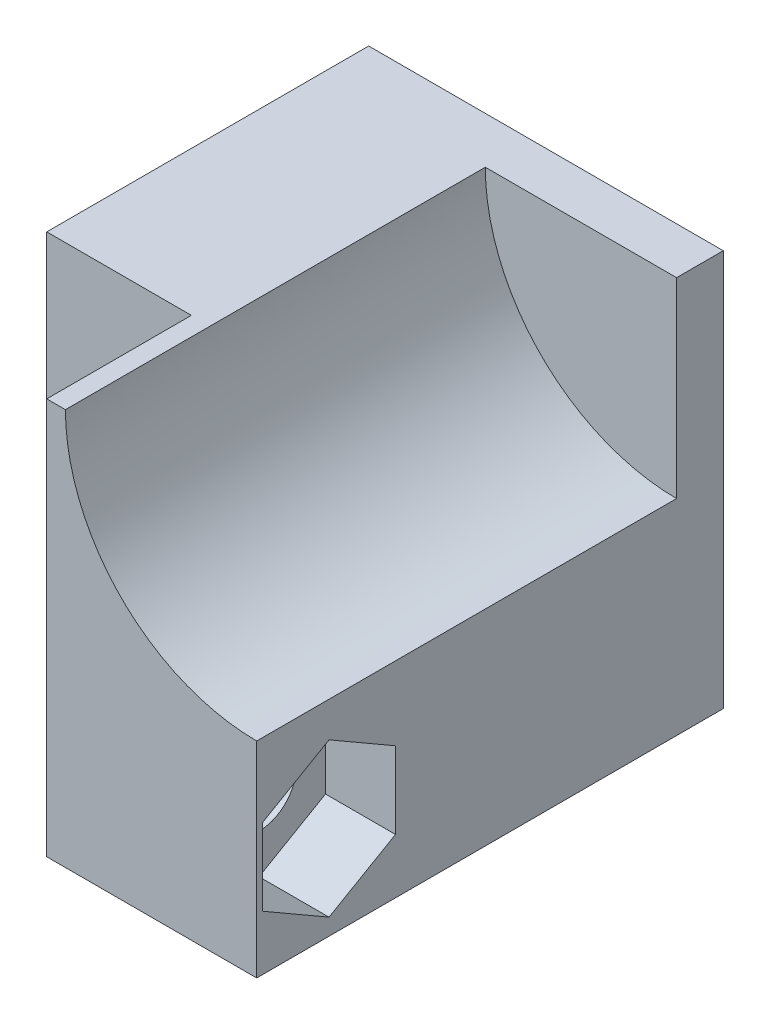
SolidWorks part; units mm, degrees
ref_plane "Alzado" through (0, 0, 0) normal (0, 0, 1) x (1, 0, 0)
ref_plane "Planta" through (0, 0, 0) normal (0, 1, 0) x (1, 0, 0)
ref_plane "Vista lateral" through (0, 0, 0) normal (1, 0, 0) x (0, 0, -1)
sketch "Croquis1" plane through (0, 0, 0) normal (0, 0, 1) x (1, 0, 0)
  line L1 (0, 0) -> (15.2, 0)
  line L2 (0, 0) -> (0, 17)
  line L3 (0, 17) -> (15.2, 17)
  line L4 (15.2, 0) -> (15.2, 17)
  dimension "D1" = 15.2
  dimension "D2" = 17
extrude "Saliente-Extruir1" add sketch "Croquis1" along normal blind 2
sketch "Croquis2" plane through (0, 0, 2) normal (0, 0, 1) x (1, 0, 0)
  line L4 (0, 17) -> (0, 0)
  line L5 (0, 0) -> (15.2, 0)
  line L6 (15.2, 0) -> (15.2, 17)
  line L7 (15.2, 17) -> (0, 17)
  line L8 (0, 17) -> (0, 0)
  line L9 (0, 0) -> (15.2, 0)
  line L10 (15.2, 0) -> (15.2, 8.8)
  line L11 (7, 17) -> (0, 17)
  arc A0 (7, 17) -> (15.2, 8.8) centre (15.2, 17) ccw
  dimension "D2" = 8.2
  dimension "D1" = 0
extrude "Saliente-Extruir2" add sketch "Croquis2" along normal blind 11.8
sketch "Croquis3" plane through (0, 0, 13.8) normal (0, 0, 1) x (1, 0, 0)
  line L0 (6.2, 17) -> (6.2, 0)
  line L1 (0, 17) -> (0, 0) construction
  line L4 (7, 17) -> (0, 17)
  line L5 (0, 17) -> (0, 0)
  line L6 (0, 0) -> (15.2, 0)
  line L7 (15.2, 0) -> (15.2, 8.8)
  line L8 (7, 17) -> (6.2, 17)
  line L10 (6.2, 0) -> (15.2, 0)
  line L11 (15.2, 0) -> (15.2, 8.8)
  arc A1 (7, 17) -> (15.2, 8.8) centre (15.2, 17) ccw
  arc A2 (7, 17) -> (15.2, 8.8) centre (15.2, 17) ccw
  dimension "D2" = 6.2
  dimension "D1" = 0
extrude "Saliente-Extruir3" add sketch "Croquis3" along normal blind 6.2
sketch "Croquis4" plane through (6.2, 0, 0) normal (-1, 0, 0) x (0, 0, 1)
  line L0 (16.9, 4) -> (16.9, 0) construction
  line L1 (20, 0) -> (13.8, 0) construction
  circle A0 centre (16.9, 4) radius 1.6
  dimension "D1" = 3.2
  dimension "D2" = 4
extrude "Cortar-Extruir1" cut sketch "Croquis4" against normal up to next
sketch "Croquis5" plane through (15.2, 0, 0) normal (1, 0, 0) x (0, 0, -1)
  line L1 (-16.9, 0.7091) -> (-14.05, 2.3546)
  line L2 (-14.05, 2.3546) -> (-14.05, 5.6454)
  line L3 (-14.05, 5.6454) -> (-16.9, 7.2909)
  line L4 (-16.9, 7.2909) -> (-19.75, 5.6454)
  line L5 (-19.75, 5.6454) -> (-19.75, 2.3546)
  line L6 (-19.75, 2.3546) -> (-16.9, 0.7091)
  circle A0 centre (-16.9, 4) radius 2.85 construction
  dimension "D1" = 5.7
extrude "Cortar-Extruir2" cut sketch "Croquis5" against normal blind 3
